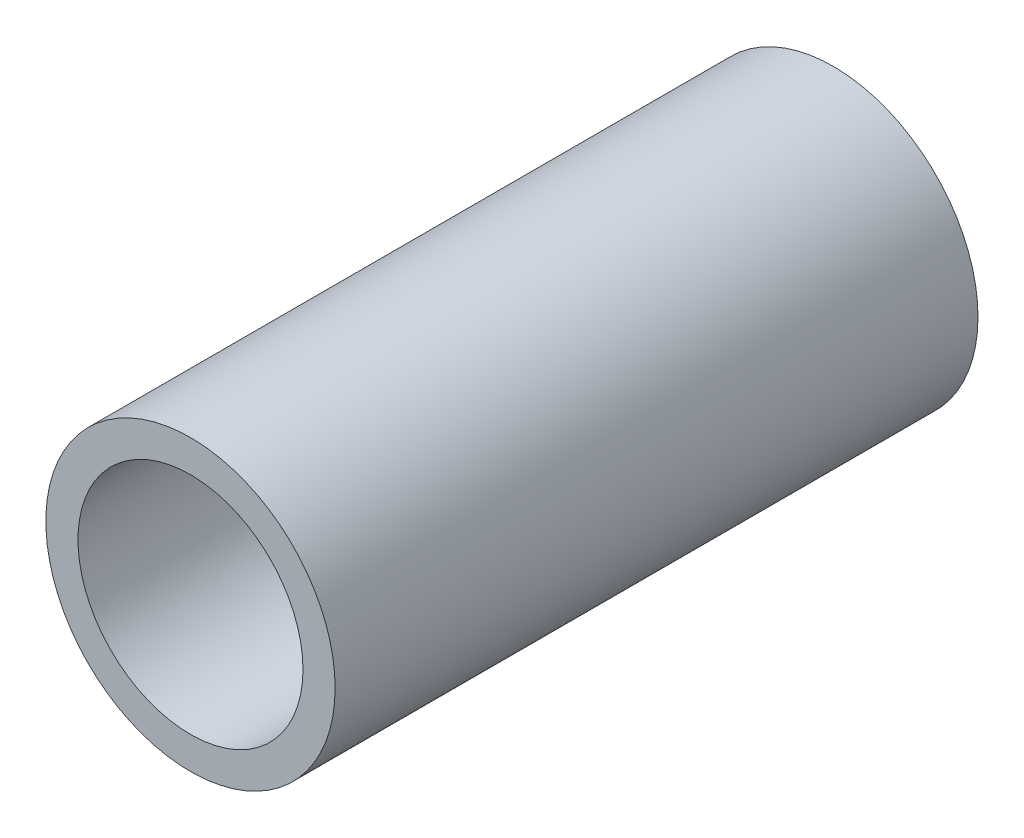
SolidWorks part; units mm, degrees
ref_plane "Front Plane" through (0, 0, 0) normal (0, 0, 1) x (1, 0, 0)
ref_plane "Top Plane" through (0, 0, 0) normal (0, 1, 0) x (1, 0, 0)
ref_plane "Right Plane" through (0, 0, 0) normal (1, 0, 0) x (0, 0, -1)
sketch "Sketch1" plane through (0, 0, 0) normal (0, 0, 1) x (1, 0, 0)
  circle A0 centre (0, 0) radius 9
  circle A1 centre (0, 0) radius 7
  dimension "D1" = 18
  dimension "D2" = 14
extrude "Boss-Extrude1" add sketch "Sketch1" along normal mid plane 40
